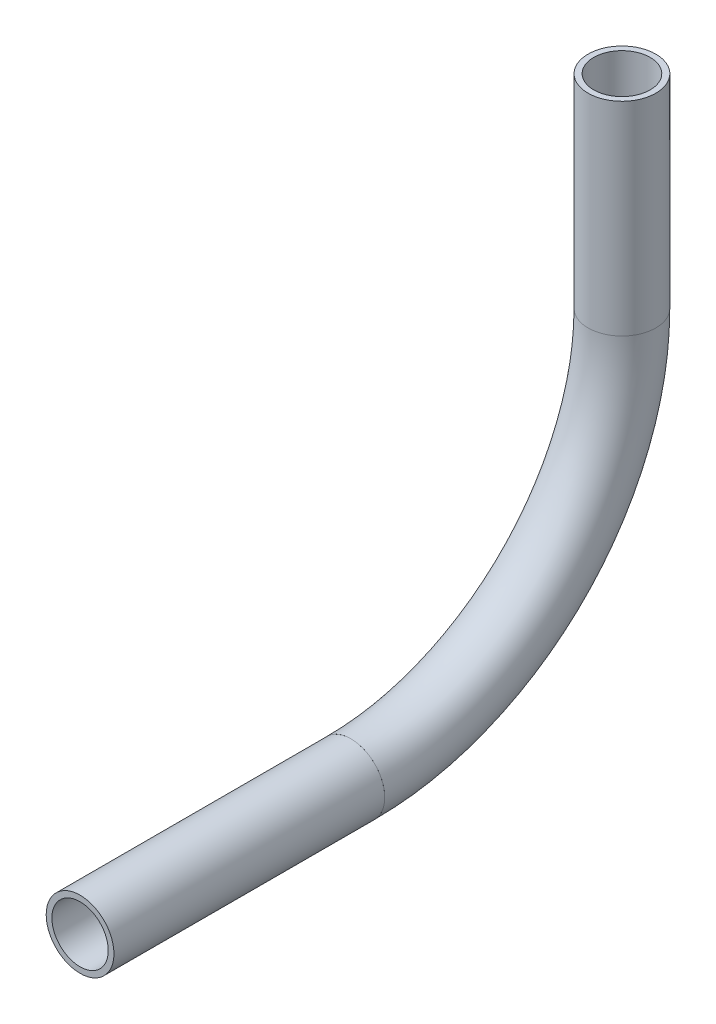
SolidWorks part; units mm, degrees
ref_plane "Front Plane" through (0, 0, 0) normal (0, 0, 1) x (1, 0, 0)
ref_plane "Top Plane" through (0, 0, 0) normal (0, 1, 0) x (1, 0, 0)
ref_plane "Right Plane" through (0, 0, 0) normal (1, 0, 0) x (0, 0, -1)
sketch "Sketch3" plane through (0, 0, 0) normal (1, 0, 0) x (0, 0, -1)
  line L0 (-259.1796, -187.6805) -> (-259.1796, -225.7805)
  line L1 (-309.9796, -276.5805) -> (-360.7276, -276.5805)
  arc A0 (-259.1796, -225.7805) -> (-309.9796, -276.5805) centre (-309.9796, -225.7805) cw
  dimension "D1" = 50.8
  dimension "D2" = 50.7481
  dimension "D3" = 38.1
other "Pipe 0.5 SCH 40(1)"
ref_plane "Plane1" through (0, -187.6805, 259.1796) normal (0, -1, 0) x (0, 0, -1)
sketch "Sketch1" plane through (0, -187.6805, 259.1796) normal (0, -1, 0) x (0, 0, -1)
  circle A0 centre (0, 0) radius 6.35
  circle A1 centre (0, 0) radius 5.2832
  point P5 (0, 0)
  dimension "In_dia" = 12.7
  dimension "Out_dia" = 10.5664
